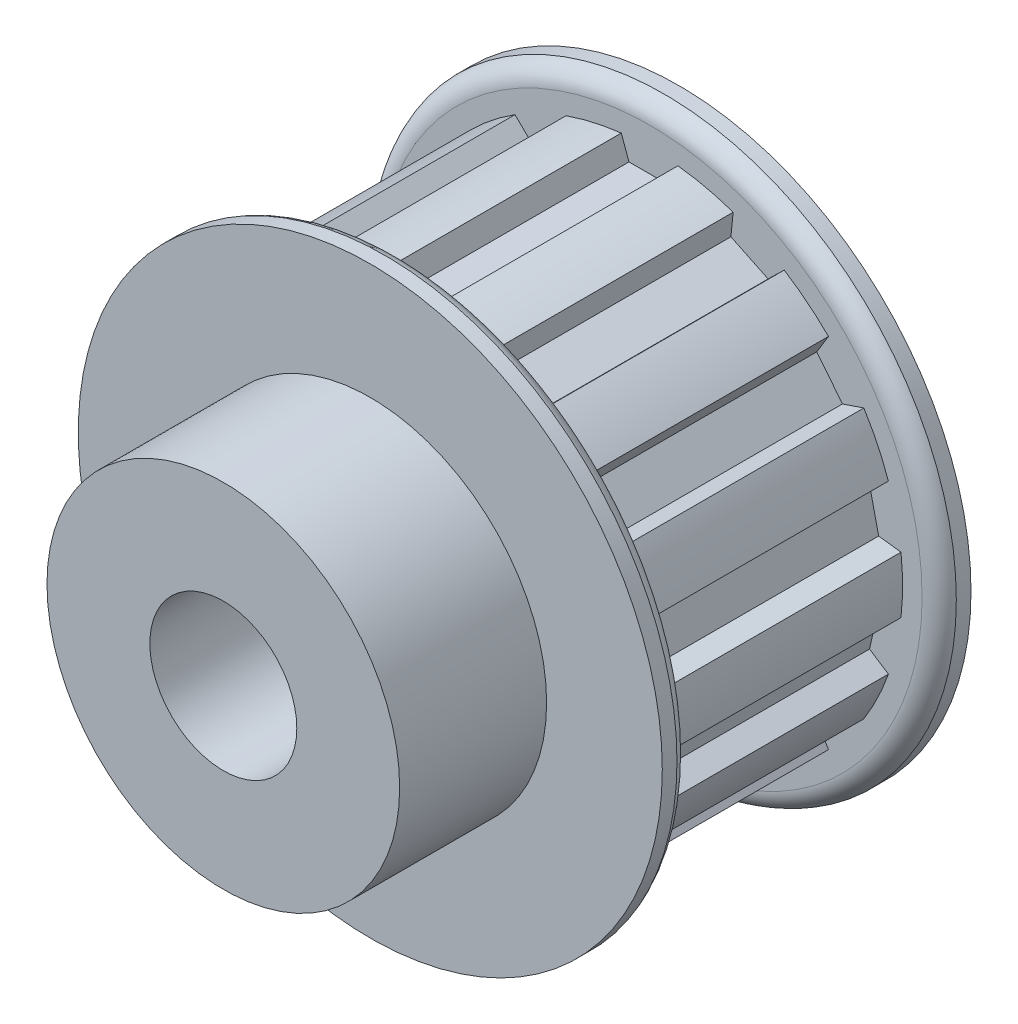
SolidWorks part; units mm, degrees
ref_plane "Front Plane" through (0, 0, 0) normal (0, 0, 1) x (1, 0, 0)
ref_plane "Top Plane" through (0, 0, 0) normal (0, 1, 0) x (1, 0, 0)
ref_plane "Right Plane" through (0, 0, 0) normal (1, 0, 0) x (0, 0, -1)
sketch "Sketch1" plane through (0, 0, 0) normal (0, 0, 1) x (1, 0, 0)
  line L0 (-3.0607, 27.1598) -> (-2.2287, 24.8738)
  line L1 (-2.2287, 24.8738) -> (2.2287, 24.8738)
  line L2 (2.2287, 24.8738) -> (3.0607, 27.1598)
  line L3 (-3.0607, 27.1598) -> (3.0607, 27.1598)
  line L4 (0, 0) -> (0, 24.8738) construction
  line L5 (0, 24.8738) -> (0, 29.4314) construction
  circle A0 centre (0, 0) radius 28.2956 construction
  circle A1 centre (0, 0) radius 31.5468 construction
  circle A2 centre (0, 0) radius 27.3317 construction
  point P6 (0, 27.1598)
  point P11 (0, 28.2956)
  point P13 (0, 31.5468)
  point P14 (0, 27.3317)
  dimension "D1" = 2.2716
  dimension "PD" = 56.5912
  dimension "D2" = 1.1358
  dimension "OD" = 63.0936
  dimension "b" = 40
  dimension "bt" = 6.1214
  dimension "ht" = 2.286
  dimension "hs" = 4.5576
sketch "Sketch2" plane through (0, 0, 0) normal (1, 0, 0) x (0, 0, -1)
  line L0 (-24.6126, 7.9375) -> (24.6126, 7.9375)
  line L1 (-24.6126, 7.9375) -> (-24.6126, 19.05)
  line L2 (-24.6126, 19.05) -> (-8.7376, 19.05)
  line L3 (-8.7376, 19.05) -> (-8.7376, 31.5468)
  line L4 (-8.7376, 31.5468) -> (-5.5626, 31.5468) construction
  line L5 (-5.5626, 31.5468) -> (-5.5626, 27.3317) construction
  line L6 (-5.5626, 27.3317) -> (21.4376, 27.3317)
  line L7 (21.4376, 27.3317) -> (21.4376, 31.5468) construction
  line L8 (21.4376, 31.5468) -> (24.6126, 31.5468) construction
  line L9 (24.6126, 31.5468) -> (24.6126, 7.9375)
  line L10 (-24.6126, 0) -> (24.6126, 0) construction
  line L13 (-8.7376, 31.5468) -> (-7.1501, 31.5468)
  line L14 (-5.5626, 29.4392) -> (-5.5626, 27.3317)
  line L15 (21.4376, 27.3317) -> (21.4376, 29.4392)
  line L16 (23.0251, 31.5468) -> (24.6126, 31.5468)
  arc A0 (-5.5626, 29.4392) -> (-7.1501, 31.5468) centre (-7.7553, 29.4392) ccw
  arc A1 (21.4376, 29.4392) -> (23.0251, 31.5468) centre (23.6303, 29.4392) cw
  point P12 (-5.5626, 29.4392)
  point P14 (-7.1501, 31.5468)
  point P20 (21.4376, 29.4392)
  point P21 (23.0251, 31.5468)
  point P25 (21.4376, 0)
  point P26 (-5.5626, 0)
  dimension "OA" = 49.2252
  dimension "Bore" = 15.875
  dimension "Hub Dia" = 38.1
  dimension "Outside Width" = 33.3502
  dimension "Inside Width" = 27.0002
revolve "Revolve1" add sketch "Sketch2" angle 360 about L10
sketch "Sketch3" plane through (0, 0, 0) normal (0, 0, 1) x (1, 0, 0)
  line L0 (-2.2287, 24.8738) -> (2.2287, 24.8738) construction
  line L1 (2.2287, 24.8738) -> (3.0607, 27.1598) construction
  line L2 (-3.0607, 27.1598) -> (-2.2287, 24.8738) construction
  line L3 (-2.2287, 24.8738) -> (2.2287, 24.8738)
  line L4 (2.2287, 24.8738) -> (3.0607, 27.1598)
  line L5 (-3.0607, 27.1598) -> (-2.2287, 24.8738)
  circle A0 centre (0, 0) radius 27.3317 construction
  arc A1 (3.0607, 27.1598) -> (-3.0607, 27.1598) centre (0, 0) ccw
extrude "Cut-Extrude1" cut sketch "Sketch3" against normal up to vertex (21.4376 mm away) from vertex at 5.5626 starting at point (0, 27.3317, 5.5626)
pattern_circular "CirPattern1" count 14 over 360 about axis through (0, 0, 0) along (0, 0, 1) of "Cut-Extrude1"
equation "\"D2@Sketch1\" = \"D1@Sketch1\"/2"
